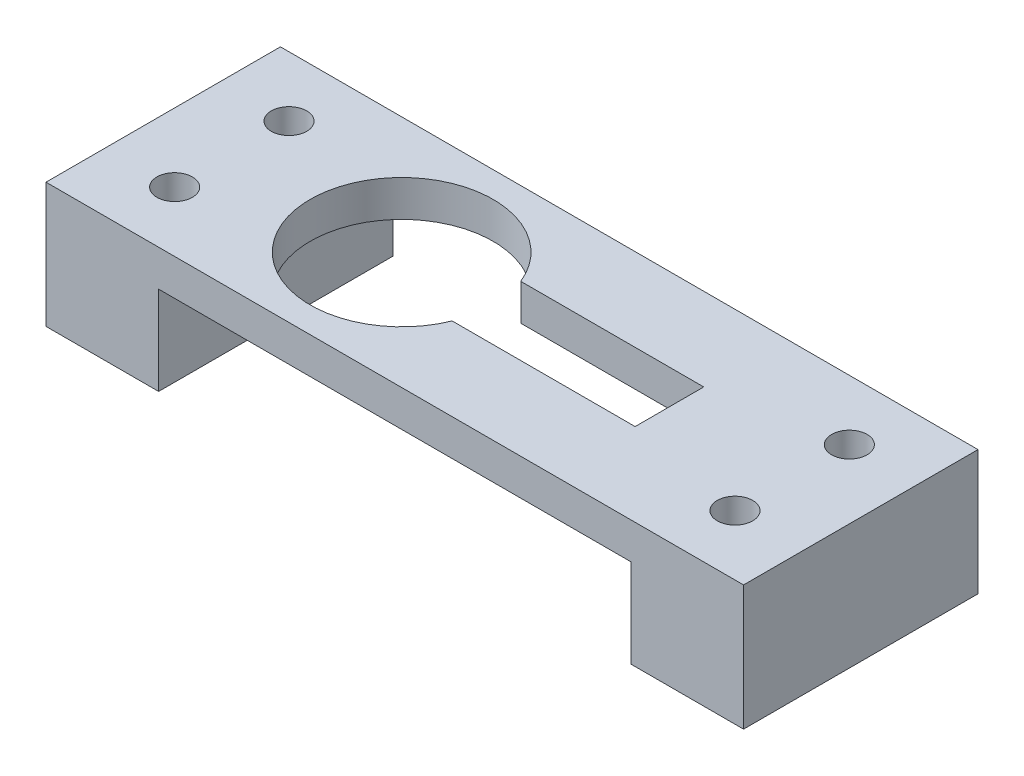
SolidWorks part; units mm, degrees
ref_plane "Front Plane" through (0, 0, 0) normal (0, 0, 1) x (1, 0, 0)
ref_plane "Top Plane" through (0, 0, 0) normal (0, 1, 0) x (1, 0, 0)
ref_plane "Right Plane" through (0, 0, 0) normal (1, 0, 0) x (0, 0, -1)
sketch "Sketch2" plane through (0, 0, 0) normal (0, 1, 0) x (1, 0, 0)
  line L0 (-24.5, 5) -> (-24.5, -5) construction
  line L1 (-30.5, 10.25) -> (30.5, 10.25)
  line L2 (-30.5, 10.25) -> (-30.5, -10.25)
  line L3 (-30.5, -10.25) -> (30.5, -10.25)
  line L4 (30.5, 10.25) -> (30.5, -10.25)
  line L5 (-30.5, 10.25) -> (30.5, -10.25) construction
  line L6 (-30.5, -10.25) -> (30.5, 10.25) construction
  line L7 (-24.5, -5) -> (24.5, -5) construction
  line L8 (24.5, -5) -> (24.5, 5) construction
  line L9 (24.5, 5) -> (-24.5, 5) construction
  line L10 (-20.65, 10.25) -> (-20.65, -10.25) construction
  line L11 (-2.2338, 3) -> (13.7662, 3)
  line L12 (-2.2338, 3) -> (-2.2338, -3)
  line L13 (-2.2338, -3) -> (13.7662, -3)
  line L14 (13.7662, 3) -> (13.7662, -3)
  line L15 (20.65, 10.25) -> (20.65, -10.25) construction
  line L16 (-20.65, 0) -> (20.65, 0) construction
  circle A0 centre (-9.65, 0) radius 8
  circle A1 centre (-24.5, 5) radius 1.55
  circle A2 centre (-24.5, -5) radius 1.55
  circle A3 centre (24.5, 5) radius 1.55
  circle A4 centre (24.5, -5) radius 1.55
  point P0 (0, 0)
  point P16 (-24.5, 0)
  point P17 (0, 5)
  point P18 (-2.2338, 0)
  point P27 (0, 0)
  dimension "D1" = 16
  dimension "D2" = 3.1
  dimension "D9" = 41.3
  dimension "D10" = 11
  dimension "D3" = 6
  dimension "D4" = 10
  dimension "D5" = 49
  dimension "D6" = 20.5
  dimension "D7" = 6
  dimension "D8" = 16
extrude "Boss-Extrude1" add sketch "Sketch2" along normal blind 3.175 contours L4 L1 L2 L3 A4 A3 A2 A1 A0 L11 L14 L13
sketch "Sketch3" plane through (0, 0, 0) normal (0, -1, 0) x (1, 0, 0)
  line L0 (-20.65, 10.25) -> (-20.65, -10.25)
  line L1 (-30.5, 10.25) -> (30.5, 10.25) construction
  line L2 (-30.5, -10.25) -> (30.5, -10.25) construction
  line L3 (-20.65, -10.25) -> (-30.5, -10.25)
  line L4 (-30.5, -10.25) -> (-30.5, 10.25)
  line L5 (-30.5, 10.25) -> (-20.65, 10.25)
  line L6 (20.65, 10.25) -> (20.65, -10.25)
  line L7 (20.65, -10.25) -> (30.5, -10.25)
  line L8 (30.5, -10.25) -> (30.5, 10.25)
  line L9 (30.5, 10.25) -> (20.65, 10.25)
  line L10 (-30.5, 10.25) -> (30.5, 10.25) construction
  circle A0 centre (-24.5, -5) radius 1.55
  circle A1 centre (-24.5, 5) radius 1.55
  circle A2 centre (24.5, -5) radius 1.55
  circle A3 centre (24.5, 5) radius 1.55
extrude "Boss-Extrude2" add sketch "Sketch3" along normal blind 7.75
